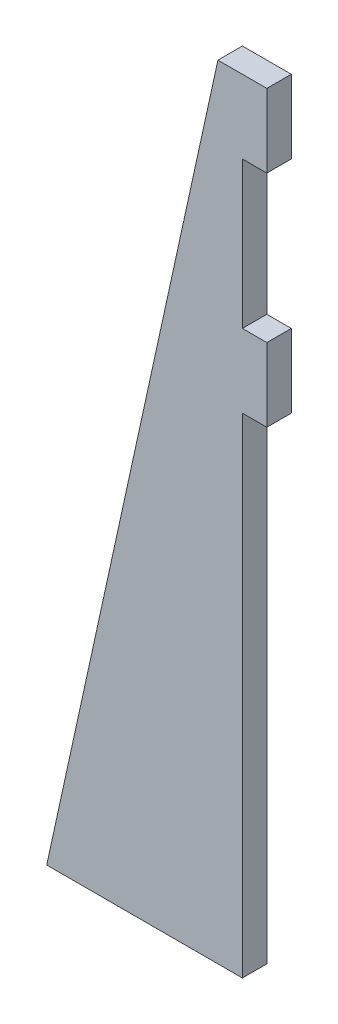
SolidWorks part; units mm, degrees
material "Plain Carbon Steel"
ref_plane "Front Plane" through (0, 0, 0) normal (0, 0, 1) x (1, 0, 0)
ref_plane "Top Plane" through (0, 0, 0) normal (0, 1, 0) x (1, 0, 0)
ref_plane "Right Plane" through (0, 0, 0) normal (1, 0, 0) x (0, 0, -1)
sketch "Sketch1" plane through (0, 0, 0) normal (0, 0, 1) x (1, 0, 0)
  line L0 (0, 0) -> (-25.4, 0)
  line L1 (0, 101.6) -> (-3.175, 101.6)
  line L2 (0, 101.6) -> (0, 0)
  line L3 (-3.175, 101.6) -> (-25.4, 0)
  line L4 (0, 101.6) -> (3.175, 101.6)
  line L5 (0, 101.6) -> (0, 92.075)
  line L6 (0, 92.075) -> (3.175, 92.075)
  line L7 (3.175, 101.6) -> (3.175, 92.075)
  line L8 (0, 73.025) -> (3.175, 73.025)
  line L9 (0, 73.025) -> (0, 63.5)
  line L10 (0, 63.5) -> (3.175, 63.5)
  line L11 (3.175, 73.025) -> (3.175, 63.5)
  dimension "D1" = 25.4
  dimension "D2" = 63.5
  dimension "D3" = 9.525
  dimension "D4" = 19.05
  dimension "D5" = 9.525
  dimension "D6" = 3.175
  dimension "D7" = 3.175
  dimension "D8" = 3.175
extrude "Boss-Extrude1" add sketch "Sketch1" along normal blind 3.175 contours L1 L3 L0 L2 | L11 L8 L2 L10 | L7 L4 L2 L6
